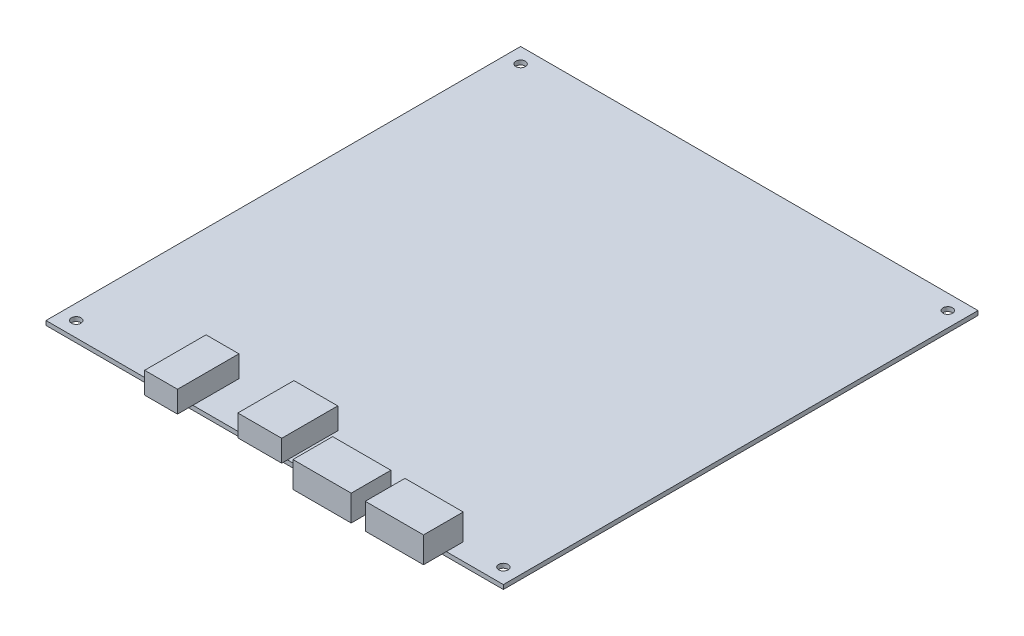
SolidWorks part; units mm, degrees
material "Copper"
ref_plane "Front Plane" through (0, 0, 0) normal (0, 0, 1) x (1, 0, 0)
ref_plane "Top Plane" through (0, 0, 0) normal (0, 1, 0) x (1, 0, 0)
ref_plane "Right Plane" through (0, 0, 0) normal (1, 0, 0) x (0, 0, -1)
sketch "Sketch1" plane through (0, 0, 0) normal (0, 1, 0) x (1, 0, 0)
  line L1 (-44.0443, 99.9438) -> (61.9557, 99.9438)
  line L2 (-44.0443, 99.9438) -> (-44.0443, -10.0562)
  line L3 (-44.0443, -10.0562) -> (61.9557, -10.0562)
  line L4 (61.9557, 99.9438) -> (61.9557, -10.0562)
  circle A0 centre (-40.5443, -6.5562) radius 1.1
  circle A1 centre (58.4557, -6.5562) radius 1.1
  circle A2 centre (-40.5443, 96.4438) radius 1.1
  circle A3 centre (58.4557, 96.4438) radius 1.1
  dimension "D3" = 2.2
  dimension "D4" = 3.5
  dimension "D6" = 3.5
  dimension "D8" = 2.2
  dimension "D11" = 2.2
  dimension "D14" = 2.2
  dimension "D1" = 110
  dimension "D2" = 106
  dimension "D5" = 3.5
  dimension "D7" = 3.5
  dimension "D9" = 3.5
  dimension "D10" = 3.5
  dimension "D12" = 3.5
  dimension "D13" = 3.5
extrude "Boss-Extrude1" add sketch "Sketch1" along normal blind 1
sketch3d "3DSketch1"
  line L0 (-44.0443, 1, 10.0562) -> (61.9557, 1, 10.0562) construction
  line L1 (-17.6243, 1, -0.6138) -> (-10.0043, 1, -0.6138)
  line L2 (-17.6243, 1, -0.6138) -> (-17.6243, 1, 13.6162)
  line L3 (-17.6243, 1, 13.6162) -> (-10.0043, 1, 13.6162)
  line L4 (-10.0043, 1, -0.6138) -> (-10.0043, 1, 13.6162)
  line L5 (-44.0443, 1, -99.9438) -> (-44.0443, 1, 10.0562) construction
  dimension "D1" = 7.62
  dimension "D2" = 10.67
  dimension "D3" = 3.56
  dimension "D4" = 26.42
extrude "Boss-Extrude3" add sketch "3DSketch1" along direction (0, 1, 0) on the side against the normal blind 5
sketch "Sketch3" plane through (0, 1, 0) normal (0, 1, 0) x (1, 0, 0)
  line L0 (-10.0043, -10.0562) -> (61.9557, -10.0562) construction
  line L1 (1.7457, 1.6138) -> (11.9057, 1.6138)
  line L2 (1.7457, 1.6138) -> (1.7457, -11.3862)
  line L3 (1.7457, -11.3862) -> (11.9057, -11.3862)
  line L4 (11.9057, 1.6138) -> (11.9057, -11.3862)
  line L5 (-10.0043, -10.0562) -> (-10.0043, 0.6138) construction
  dimension "D1" = 11.67
  dimension "D2" = 1.33
  dimension "D3" = 10.16
  dimension "D4" = 11.75
extrude "Boss-Extrude4" add sketch "Sketch3" along normal blind 5
sketch "Sketch4" plane through (0, 1, 0) normal (0, 1, 0) x (-1, 0, 0)
  line L0 (-35.2357, 6.1462) -> (-48.7357, 6.1462)
  line L1 (-18.4757, 6.1462) -> (-31.9757, 6.1462)
  line L2 (-18.4757, 6.1462) -> (-18.4757, 15.3462)
  line L3 (-18.4757, 15.3462) -> (-31.9757, 15.3462)
  line L4 (-31.9757, 6.1462) -> (-31.9757, 15.3462)
  line L5 (-35.2357, 6.1462) -> (-35.2357, 15.3462)
  line L6 (-35.2357, 15.3462) -> (-48.7357, 15.3462)
  line L7 (-48.7357, 6.1462) -> (-48.7357, 15.3462)
  line L8 (-11.9057, 10.0562) -> (-11.9057, -1.6138) construction
  line L9 (-11.9057, 10.0562) -> (-61.9557, 10.0562) construction
  dimension "D1" = 9.2
  dimension "D2" = 13.5
  dimension "D3" = 13.5
  dimension "D4" = 3.26
  dimension "D5" = 0
  dimension "D6" = 9.2
  dimension "D7" = 6.57
  dimension "D8" = 5.29
extrude "Boss-Extrude5" add sketch "Sketch4" along normal blind 6
